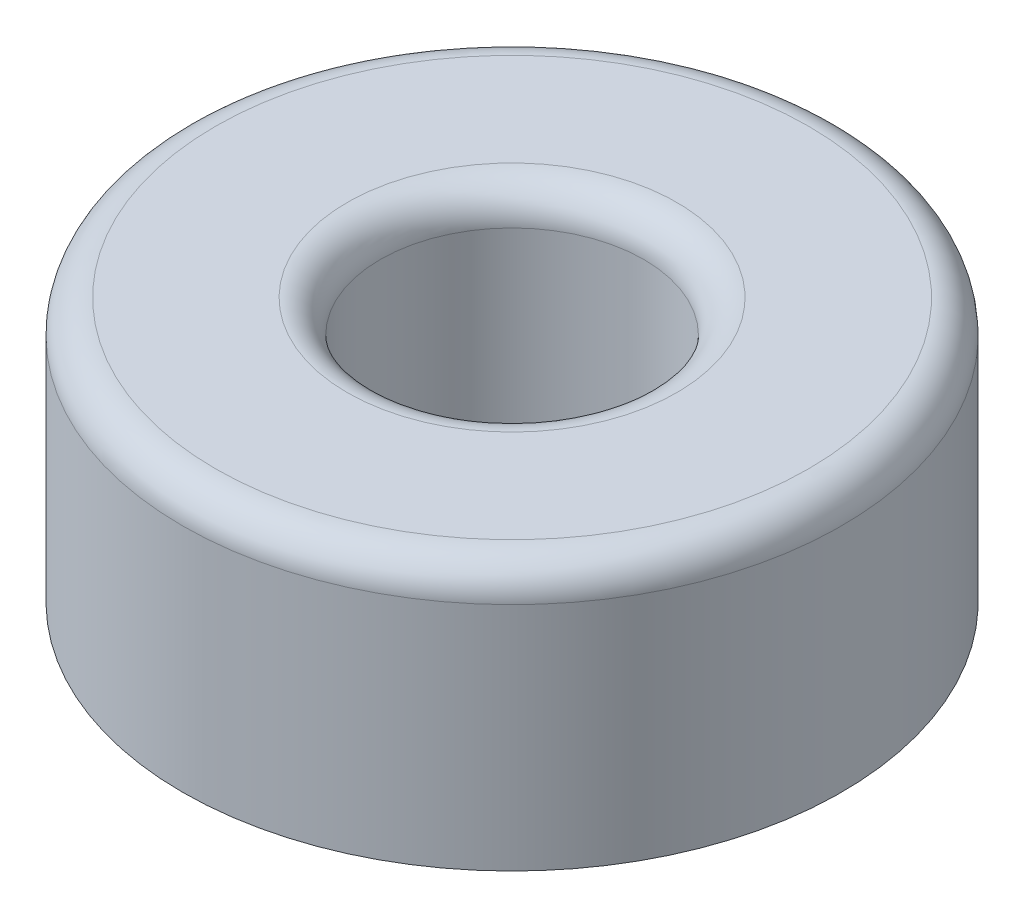
SolidWorks part; units mm, degrees
ref_plane "Front Plane" through (0, 0, 0) normal (0, 0, 1) x (1, 0, 0)
ref_plane "Top Plane" through (0, 0, 0) normal (0, 1, 0) x (1, 0, 0)
ref_plane "Right Plane" through (0, 0, 0) normal (1, 0, 0) x (0, 0, -1)
sketch "Sketch1" plane through (0, 0, 0) normal (0, 1, 0) x (1, 0, 0)
  circle A0 centre (0, 0) radius 2
  circle A1 centre (0, 0) radius 5
  dimension "D1" = 4
  dimension "D2" = 10
extrude "Boss-Extrude1" add sketch "Sketch1" along normal blind 4
fillet "Fillet2" radius 0.5 2 edges at (0, 4, 2) (0, 4, 5)
